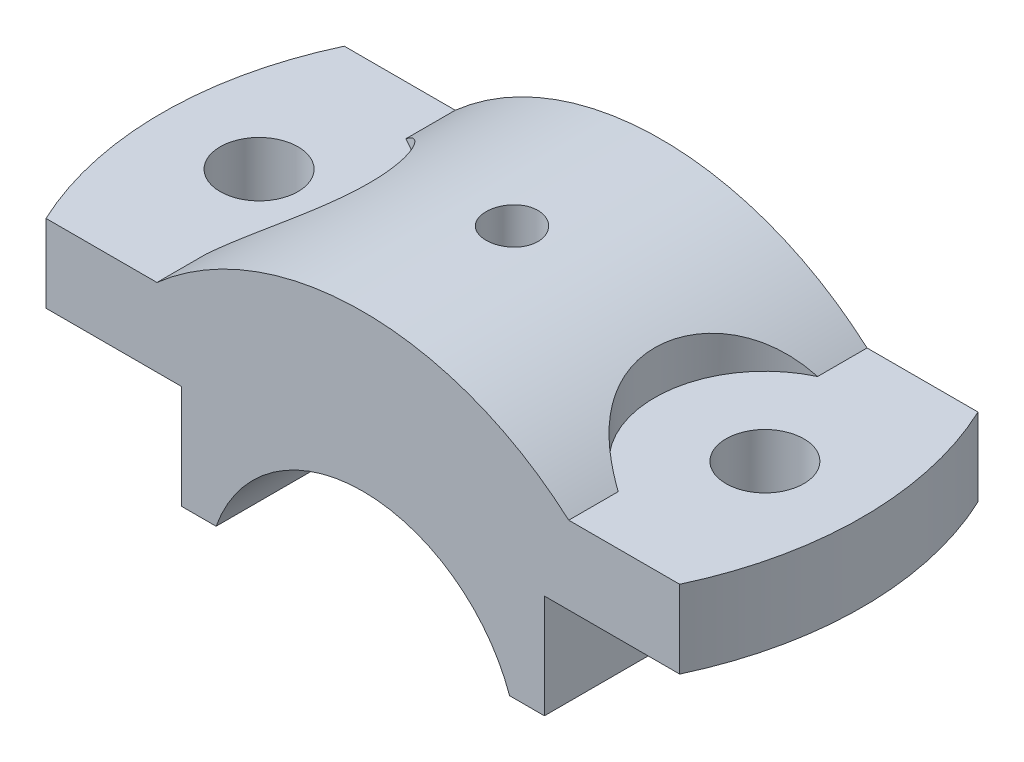
SolidWorks part; units mm, degrees
ref_plane "Front Plane" through (0, 0, 0) normal (0, 0, 1) x (1, 0, 0)
ref_plane "Top Plane" through (0, 0, 0) normal (0, 1, 0) x (1, 0, 0)
ref_plane "Right Plane" through (0, 0, 0) normal (1, 0, 0) x (0, 0, -1)
sketch "Sketch1" plane through (0, 0, 0) normal (0, 0, 1) x (1, 0, 0)
  line L0 (0, 0) -> (0, 50000) construction
  line L2 (31.749, 36) -> (31.749, 24)
  line L3 (-31.749, 36) -> (-31.749, 24)
  line L4 (-28, 24) -> (-28, 8)
  line L5 (-31.749, 24) -> (-28, 24)
  line L6 (-28, 8) -> (-22.6274, 8)
  line L7 (28, 8) -> (22.6274, 8)
  line L8 (31.749, 24) -> (28, 24)
  line L9 (28, 24) -> (28, 8)
  arc A0 (31.749, 36) -> (-31.749, 36) centre (0, 0) ccw
  arc A1 (22.6274, 8) -> (-22.6274, 8) centre (0, 0) ccw
  point P9 (0, 36)
  dimension "D1" = 96
  dimension "D2" = 48
  dimension "D6" = 28
  dimension "D7" = 16
extrude "Boss-Extrude1" add sketch "Sketch1" along normal mid plane 46
sketch "Sketch3" plane through (0, 0, 0) normal (0, 1, 0) x (1, 0, 0)
  line L0 (31.749, -23) -> (31.749, 23) construction
  line L1 (31.749, -23) -> (31.749, 23)
  line L2 (31.749, 23) -> (48.8569, 23)
  line L3 (31.749, -23) -> (48.8569, -23)
  arc A0 (48.8569, -23) -> (48.8569, 23) centre (0, 0) ccw
  dimension "D1" = 108
extrude "Boss-Extrude4" add sketch "Sketch3" along normal blind 12 from offset 24
mirror "Mirror2" about plane through (0, 0, 0) normal (1, 0, 0) of "Boss-Extrude4"
sketch "Sketch4" plane through (0, 36, 0) normal (0, 1, 0) x (1, 0, 0)
  circle A0 centre (0, 0) radius 3
  dimension "D1" = 6
extrude "Cut-Extrude1" cut sketch "Sketch4" against normal through all both and the other way through all
ref_plane "Plane1" through (0, 48, 0) normal (0, 1, 0) x (1, 0, 0)
sketch "Sketch5" plane through (0, 48, 0) normal (0, 1, 0) x (1, 0, 0)
  circle A0 centre (0, 0) radius 4
  dimension "D1" = 8
extrude "Cut-Extrude2" cut sketch "Sketch5" against normal blind 16
hole_wizard "Ø12.0mm Dowel Hole1" positions "Sketch6" profile "Sketch7" hole size "Ø12.0" standard "ISO" end condition through all
sketch "Sketch6" plane through (0, 36, 0) normal (0, 1, 0) x (1, 0, 0)
  line L0 (-48.8569, 23) -> (-31.749, 23) construction
  line L1 (48.8569, 23) -> (31.749, 23) construction
  point P0 (-39, 0)
  point P2 (39, 0)
  dimension "D1" = 39
  dimension "D2" = 39
  dimension "D3" = 23
  dimension "D4" = 23
sketch "Sketch7" plane through (-39, 36, 0) normal (1, 0, 0) x (0, 0, 1)
  line L0 (0, 0) -> (0, 28)
  line L1 (0, 28) -> (6, 28)
  line L2 (6, 28) -> (6, 0)
  line L5 (6, 0) -> (0, 0)
  line L11 (0, -6.35) -> (0, 107.95) construction
  dimension "Thru Hole Dia." = 12
  dimension "Thru Hole Depth" = 28
sketch "Sketch8" plane through (0, 36, 0) normal (0, 1, 0) x (1, 0, 0)
  line L0 (31.749, -23) -> (31.749, 23) construction
  line L1 (31.749, -15.3761) -> (31.749, 15.3761)
  arc A0 (31.749, 15.3761) -> (31.749, -15.3761) centre (39, 0) ccw
  dimension "D1" = 34
extrude "Cut-Extrude3" cut sketch "Sketch8" along normal blind 16
mirror "Mirror3" about plane through (0, 0, 0) normal (1, 0, 0) of "Cut-Extrude3"
